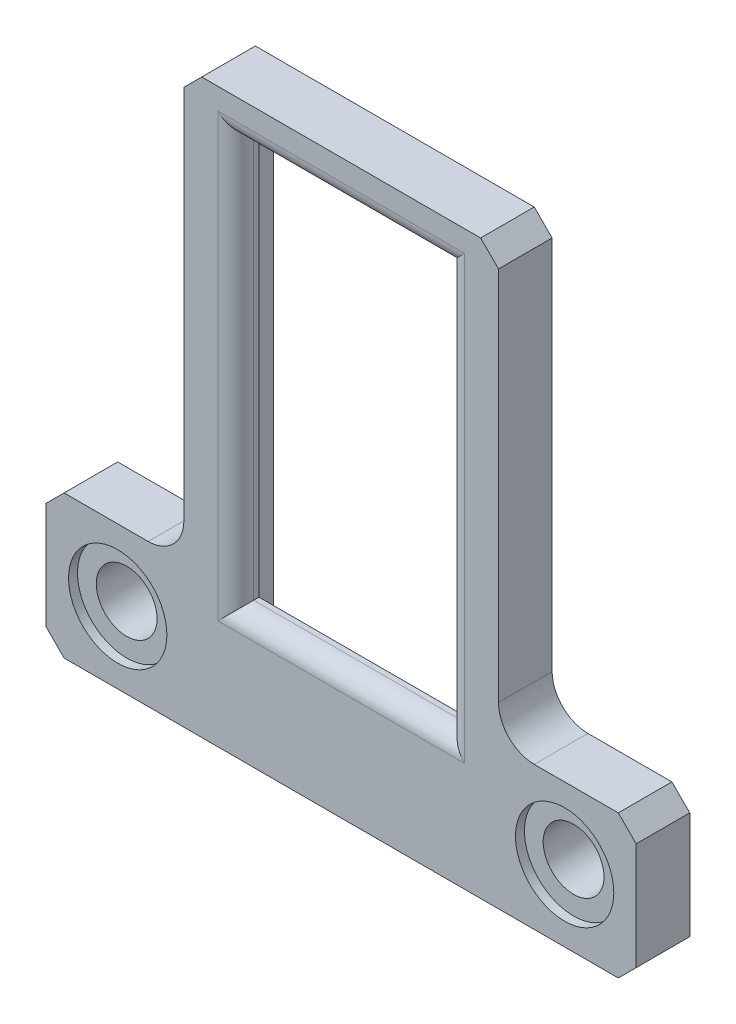
SolidWorks part; units mm, degrees
ref_plane "前视基准面" through (0, 0, 0) normal (0, 0, 1) x (1, 0, 0)
ref_plane "上视基准面" through (0, 0, 0) normal (0, 1, 0) x (1, 0, 0)
ref_plane "右视基准面" through (0, 0, 0) normal (1, 0, 0) x (0, 0, -1)
other "Configuration Table"
sketch "草图1" plane through (0, 0, 0) normal (0, 0, 1) x (1, 0, 0)
  line L0 (-7.7, -32) -> (25.3, -32)
  line L1 (0, 0) -> (17.6, 0)
  line L2 (0, 0) -> (0, -24)
  line L4 (17.6, 0) -> (17.6, -24)
  line L7 (17.6, -24) -> (25.3, -24)
  line L8 (25.3, -32) -> (25.3, -24)
  line L11 (0, -24) -> (-7.7, -24)
  line L12 (-7.7, -32) -> (-7.7, -24)
  dimension "D1" = 17.6
  dimension "D2" = 33
  dimension "D3" = 7.7
  dimension "D4" = 8
  dimension "D5" = 32
  dimension "D6" = 8
extrude "凸台-拉伸1" add sketch "草图1" along normal blind 3
sketch "草图2" plane through (0, 0, 0) normal (0, 0, -1) x (-1, 0, 0)
  line L0 (0, 0) -> (0, -24) construction
  line L1 (-17.6, 0) -> (0, 0) construction
  line L6 (-15.6, -1) -> (-15.6, -30)
  line L7 (-2, -1) -> (-2, -30)
  line L13 (-2, -1) -> (-15.6, -1)
  line L16 (-2, -30) -> (-15.6, -30)
  dimension "D2" = 29
  dimension "D3" = 2
  dimension "D1" = 13.6
  dimension "D4" = 1
extrude "切除-拉伸1" cut sketch "草图2" against normal blind 1.7
sketch "草图3" plane through (0, 0, 3) normal (0, 0, 1) x (1, 0, 0)
  line L0 (17.6, 0) -> (0, 0) construction
  line L1 (2.9, -2.2) -> (14.7, -2.2)
  line L2 (2.9, -2.2) -> (2.9, -24.9)
  line L3 (2.9, -24.9) -> (14.7, -24.9)
  line L4 (14.7, -2.2) -> (14.7, -24.9)
  line L5 (17.6, -24) -> (17.6, 0) construction
  dimension "D1" = 22.7
  dimension "D2" = 11.8
  dimension "D3" = 2.2
  dimension "D4" = 2.9
extrude "切除-拉伸2" cut sketch "草图3" against normal through all
hole_wizard "M3 六角头螺栓的柱形沉头孔1" positions "草图4" profile "草图5" counterbore size "M3" standard "GB"
sketch "草图4" plane through (0, 0, 3) normal (0, 0, 1) x (1, 0, 0)
  point P0 (-3.7, -28)
  point P3 (21.3, -28)
sketch "草图5" plane through (-3.7, -28, 3) normal (1, 0, 0) x (0, -1, 0)
  line L0 (0, 0) -> (0, 8.5215)
  line L1 (0, 8.5215) -> (1.7, 7.5)
  line L2 (1.7, 7.5) -> (1.7, 0.5)
  line L3 (1.7, 0.5) -> (2.75, 0.5)
  line L4 (2.75, 0.5) -> (2.75, 0)
  line L5 (2.75, 0) -> (0, 0)
  line L10 (0, 8.5215) -> (-1.7, 7.5) construction
  line L11 (0, -6.35) -> (0, 107.95) construction
  dimension "孔直径" = 3.4
  dimension "孔深度" = 7.5
  dimension "柱形沉头孔直径" = 5.5
  dimension "柱形沉头孔深度" = 0.5
  dimension "导头角度" = 118
chamfer "倒角1" distance 1 angle 45 6 edges at (-7.7, -24, 1.5) (-7.7, -32, 1.5) (25.3, -32, 1.5) (25.3, -24, 1.5) (17.6, 0, 1.5) (0, 0, 1.5)
fillet "圆角1" radius 2 2 edges at (17.6, -24, 1.5) (0, -24, 1.5)
fillet "圆角3" radius 1 4 edges at (8.8, -24.9, 3) (14.7, -13.55, 3) (2.9, -13.55, 3) (8.8, -2.2, 3)
